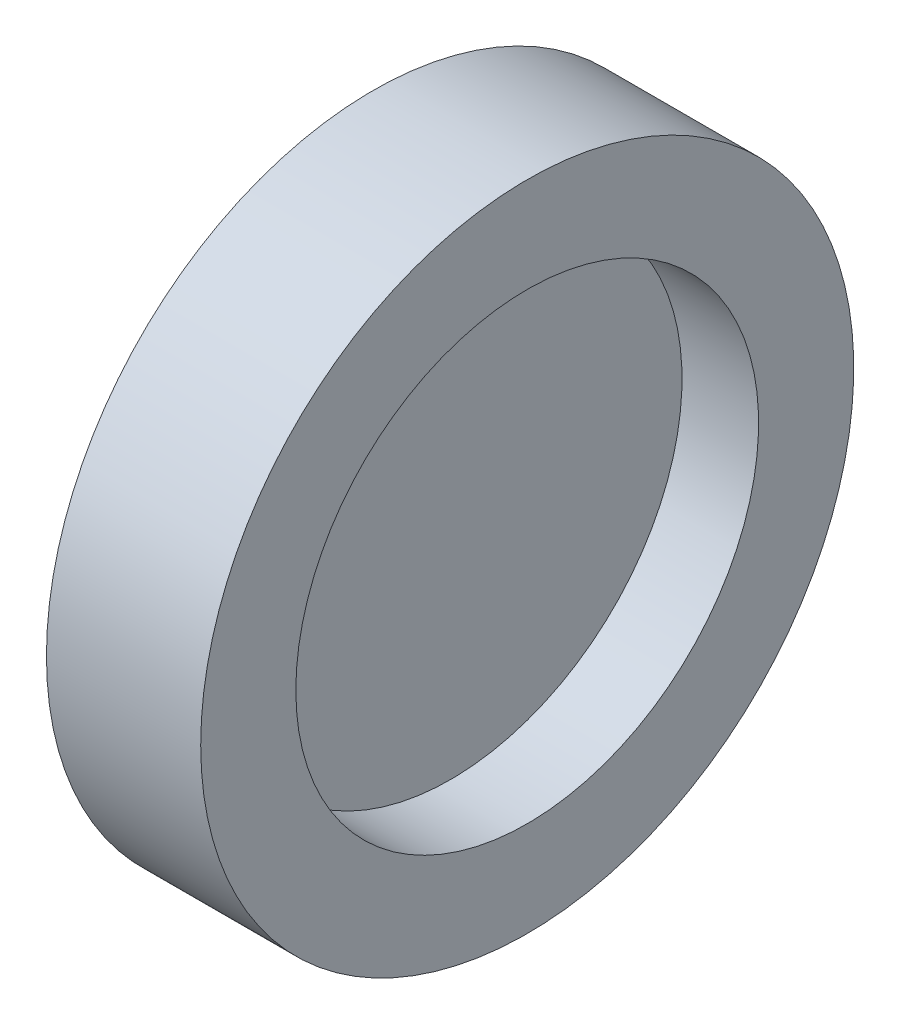
SolidWorks part; units mm, degrees
ref_plane "前视基准面" through (0, 0, 0) normal (0, 0, 1) x (1, 0, 0)
ref_plane "上视基准面" through (0, 0, 0) normal (0, 1, 0) x (1, 0, 0)
ref_plane "右视基准面" through (0, 0, 0) normal (1, 0, 0) x (0, 0, -1)
sketch "草图1" plane through (0, 0, 0) normal (0, 0, 1) x (1, 0, 0)
  line L0 (-0.0215, 9) -> (-0.0215, 0)
  line L2 (-0.0215, 9) -> (0.0215, 9)
  line L3 (-0.0215, 0) -> (0.0215, 0)
  line L4 (0.0215, 9) -> (0.0215, 0)
revolve "旋转2" add sketch "草图1" angle 360 about L3
sketch "草图4" plane through (0, 0, 0) normal (0, 0, 1) x (1, 0, 0)
  line L0 (-3, 12.7) -> (3, 12.7)
  line L1 (3, 12.7) -> (3, 9)
  line L2 (3, 9) -> (-3, 9)
  line L3 (0.0215, 9) -> (-0.0215, 9) construction
  line L4 (-3, 9) -> (-3, 12.7)
  line L5 (0, 9) -> (0, 12.7) construction
  line L6 (-1.6142, 0) -> (1.5903, 0) construction
revolve "旋转3" add sketch "草图4" angle 360 about L6
equation "\"D1@草图4\"=\"D1@草图1\""
